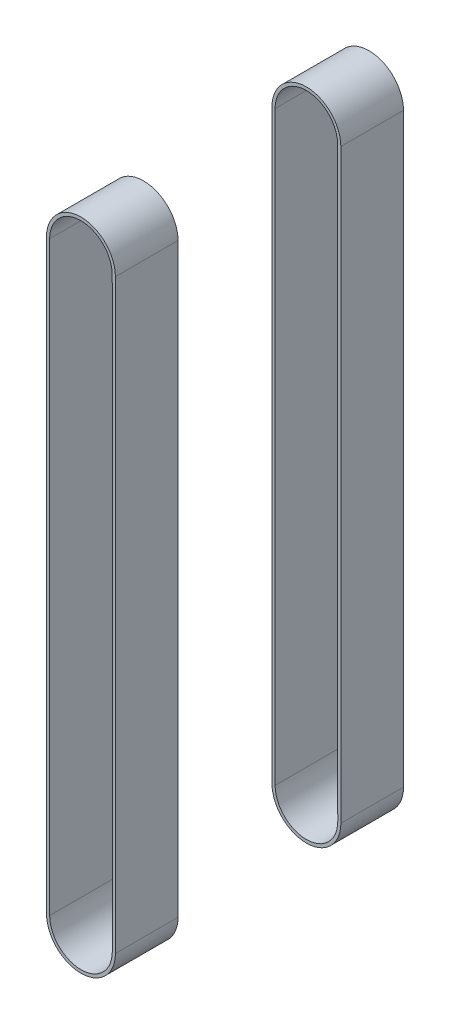
SolidWorks part; units mm, degrees
material "BUTYL"
ref_plane "Plan de face" through (0, 0, 0) normal (0, 0, 1) x (1, 0, 0)
ref_plane "Plan de dessus" through (0, 0, 0) normal (0, 1, 0) x (1, 0, 0)
ref_plane "Plan de droite" through (0, 0, 0) normal (1, 0, 0) x (0, 0, -1)
sketch "Sketch1" plane through (0, 0, 0) normal (0, 0, 1) x (1, 0, 0)
  line L0 (285.2327, 88.0782) -> (285.2416, -30.7691)
  line L1 (297.9327, 88.0792) -> (297.9416, -30.7682)
  line L2 (284.5977, 88.0781) -> (284.6066, -30.7692)
  line L3 (298.5677, 88.0792) -> (298.5766, -30.7681)
  circle A0 centre (291.5916, -30.7687) radius 6.35 construction
  circle A1 centre (291.5827, 88.0787) radius 6.35 construction
  arc A2 (285.2416, -30.7691) -> (297.9416, -30.7682) centre (291.5916, -30.7687) ccw
  arc A3 (297.9327, 88.0792) -> (285.2327, 88.0782) centre (291.5827, 88.0787) ccw
  arc A4 (284.6066, -30.7692) -> (298.5766, -30.7681) centre (291.5916, -30.7687) ccw
  arc A5 (298.5677, 88.0792) -> (284.5977, 88.0781) centre (291.5827, 88.0787) ccw
  dimension "D1" = 0.635
extrude "Boss-Extrude1" add sketch "Sketch1" along normal blind 12.7 from offset 16.51
mirror "Mirror2" about plane through (0, 0, 0) normal (0, 0, 1) of bodies 101
equation "\"Cout/Uni\"= ( ( \"Coût Achat\" + \"Coût Modif\" ) / \"Nb/Paquet\" )"
